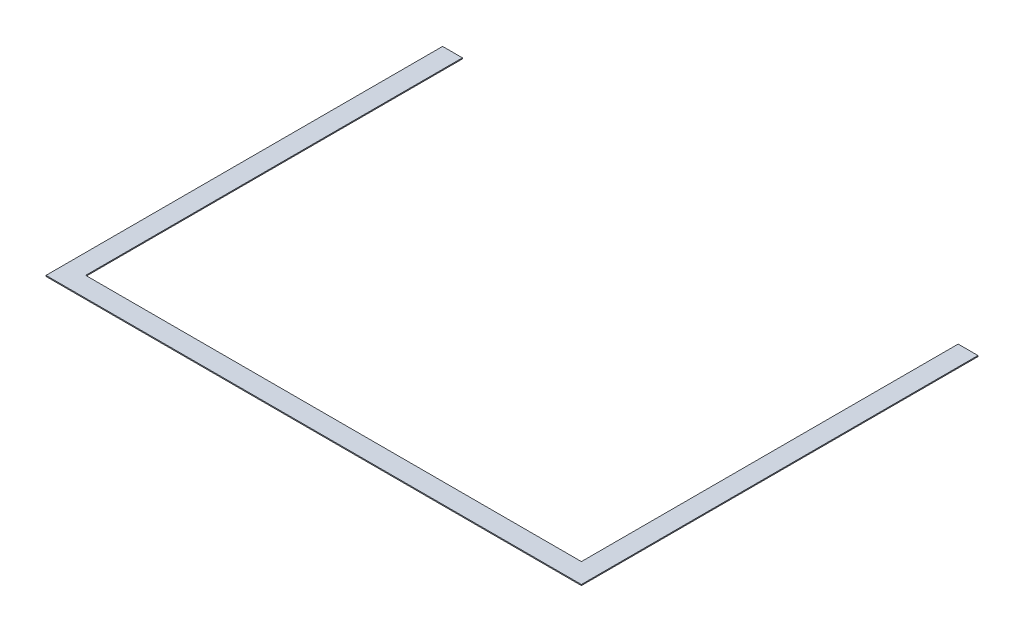
SolidWorks part; units mm, degrees
ref_plane "Front Plane" through (0, 0, 0) normal (0, 0, 1) x (1, 0, 0)
ref_plane "Top Plane" through (0, 0, 0) normal (0, 1, 0) x (1, 0, 0)
ref_plane "Right Plane" through (0, 0, 0) normal (1, 0, 0) x (0, 0, -1)
sketch "Sketch1" plane through (0, 0, 0) normal (0, 1, 0) x (1, 0, 0)
  line L1 (-106.6212, -63.3788) -> (2593.3788, -63.3788)
  line L2 (-106.6212, -63.3788) -> (-106.6212, 1936.6212)
  line L3 (-106.6212, 1936.6212) -> (-6.6212, 1936.6212)
  line L4 (2593.3788, -63.3788) -> (2593.3788, 1936.6212)
  line L6 (2493.3788, 186.6212) -> (2493.3788, 1936.6212)
  line L7 (-6.6212, 36.6212) -> (2493.3788, 36.6212)
  line L10 (2493.3788, 36.6212) -> (2493.3788, 186.6212)
  line L12 (2493.3788, 1936.6212) -> (2593.3788, 1936.6212)
  line L13 (-6.6212, 36.6212) -> (-6.6212, 1936.6212)
  point P0 (0, 0)
  point P6 (-101.6212, 101.6212)
  dimension "D2" = 2000
  dimension "D3" = 2500
  dimension "D4" = 100
  dimension "D6" = 100
extrude "Boss-Extrude1" add sketch "Sketch1" along normal blind 5
